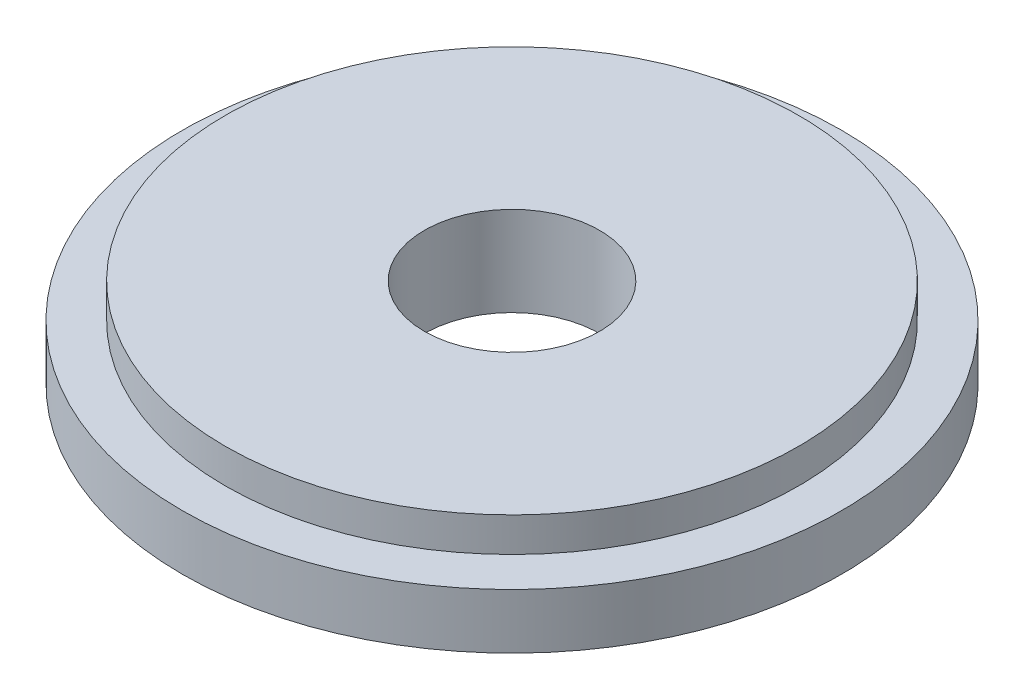
SolidWorks part; units mm, degrees
ref_plane "Front Plane" through (0, 0, 0) normal (0, 0, 1) x (1, 0, 0)
ref_plane "Top Plane" through (0, 0, 0) normal (0, 1, 0) x (1, 0, 0)
ref_plane "Right Plane" through (0, 0, 0) normal (1, 0, 0) x (0, 0, -1)
sketch "Sketch2" plane through (0, 0, 0) normal (0, 1, 0) x (1, 0, 0)
  circle A0 centre (0, 0) radius 6.8326
  dimension "D1" = 13.6652
extrude "Boss-Extrude1" add sketch "Sketch2" along normal blind 1.143
sketch "Sketch3" plane through (0, 1.143, 0) normal (0, 1, 0) x (1, 0, 0)
  circle A0 centre (0, 0) radius 5.9436
  dimension "D1" = 11.8872
extrude "Boss-Extrude2" add sketch "Sketch3" along normal blind 0.7112
sketch "Sketch4" plane through (0, 1.8542, 0) normal (0, 1, 0) x (1, 0, 0)
  circle A0 centre (0, 0) radius 1.8161
  dimension "D1" = 3.6322
extrude "Cut-Extrude1" cut sketch "Sketch4" against normal through all
